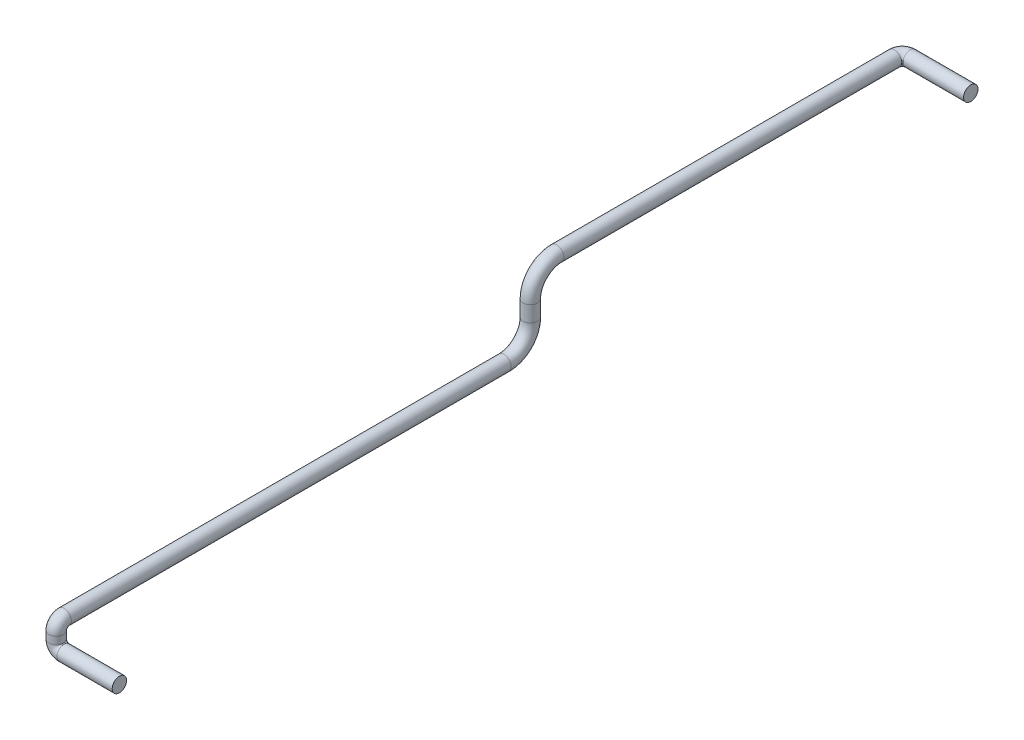
SolidWorks part; units mm, degrees
ref_plane "Alzado" through (0, 0, 0) normal (0, 0, 1) x (1, 0, 0)
ref_plane "Planta" through (0, 0, 0) normal (0, 1, 0) x (1, 0, 0)
ref_plane "Vista lateral" through (0, 0, 0) normal (1, 0, 0) x (0, 0, -1)
sketch3d "Croquis3D1"
  line L0 (0, 0, 0) -> (-105, 0, 0)
  line L1 (-120, 15, 0) -> (-120, 29, 0)
  line L2 (-120, 174, -950) -> (-120, 174, -1591)
  line L3 (-105, 174, -1606) -> (10, 174, -1606)
  line L4 (-120, 44, -15) -> (-120, 44, -850)
  line L5 (-120, 124, -900) -> (-120, 94, -900)
  arc A0 (-120, 44, -15) -> (-120, 29, 0) centre (-120, 29, -15) ccw
  arc A1 (-105, 0, 0) -> (-120, 15, 0) centre (-105, 15, 0) ccw
  arc A2 (-120, 124, -900) -> (-120, 174, -950) centre (-120, 124, -950) ccw
  arc A3 (-120, 94, -900) -> (-120, 44, -850) centre (-120, 94, -850) ccw
  arc A4 (-120, 174, -1591) -> (-105, 174, -1606) centre (-105, 174, -1591) ccw
  point P10 (-120, 44, 0)
  point P11 (-105, 29, -15)
  point P14 (-120, 0, 0)
  point P15 (-105, 15, -15)
  point P18 (-120, 174, -900)
  point P19 (-170, 124, -950)
  point P22 (-120, 44, -900)
  point P23 (-170, 94, -850)
  point P26 (-120, 174, -1606)
  point P27 (-105, 159, -1591)
  dimension "D6" = 15
  dimension "D7" = 50
  dimension "D8" = 15
  dimension "D1" = 120
  dimension "D2" = 44
  dimension "D5" = 706
  dimension "D3" = 900
  dimension "D4" = 130
  dimension "D9" = 130
sketch "Croquis1" plane through (0, 0, 0) normal (1, 0, 0) x (0, 0, -1)
  circle A0 centre (0, 0) radius 13.7
  dimension "D1" = 27.4
sweep "Barrer1" add profiles "Croquis1" path "Croquis3D1"
